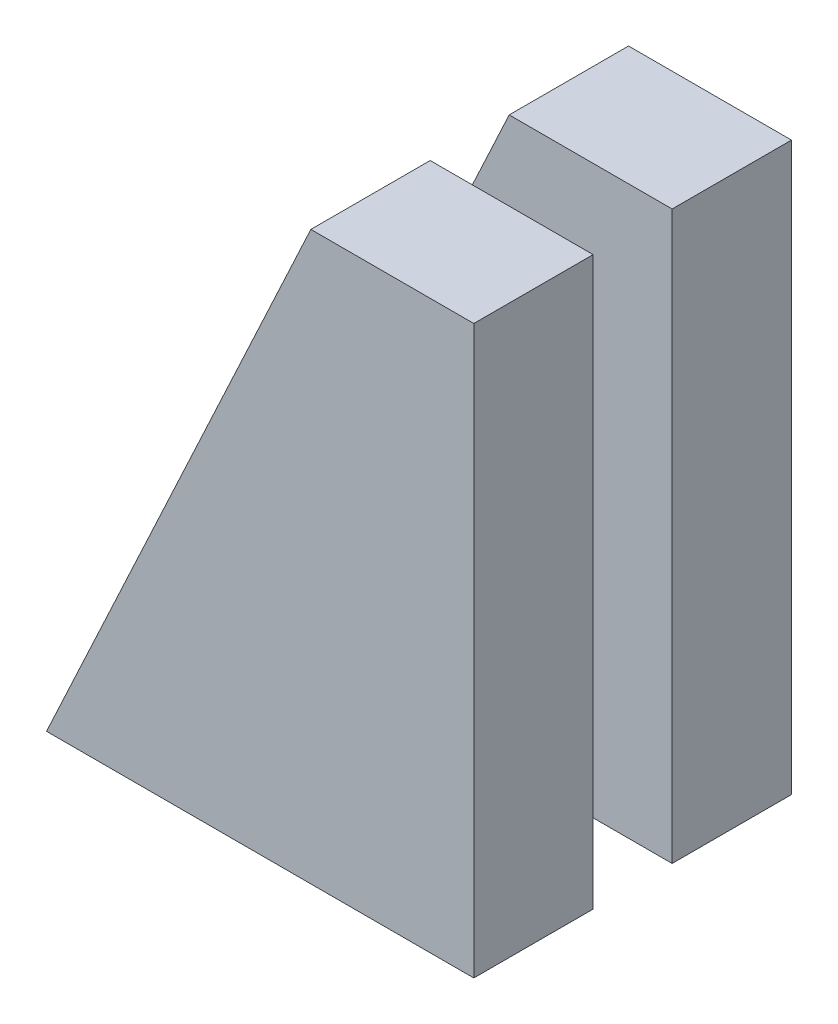
SolidWorks part; units mm, degrees
ref_plane "前视基准面" through (0, 0, 0) normal (0, 0, 1) x (1, 0, 0)
ref_plane "上视基准面" through (0, 0, 0) normal (0, 1, 0) x (1, 0, 0)
ref_plane "右视基准面" through (0, 0, 0) normal (1, 0, 0) x (0, 0, -1)
sketch "草图1" plane through (0, 0, 0) normal (0, 0, 1) x (1, 0, 0)
  line L0 (0, 0) -> (0, 635)
  line L1 (0, 635) -> (-150, 635)
  line L2 (-150, 635) -> (-446.1054, 0)
  line L3 (-446.1054, 0) -> (0, 0)
  line L4 (0, 0) -> (0, 665)
  line L5 (0, 665) -> (-191.1797, 665)
  line L6 (-191.1797, 665) -> (-501.2743, 0)
  line L7 (-501.2743, 0) -> (-446.1054, 0)
  dimension "D1" = 150
  dimension "D2" = 635
  dimension "D3" = 65
  dimension "D4" = 30
  dimension "D5" = 50
extrude "凸台-拉伸1" add sketch "草图1" along normal blind 140 contours L2 L3 L0 L1 | L6 L7 L2 L1 L4 L5
pattern_linear "阵列(线性)1" count 2 spacing 232.7 along (0, 0, 1) of "凸台-拉伸1"
